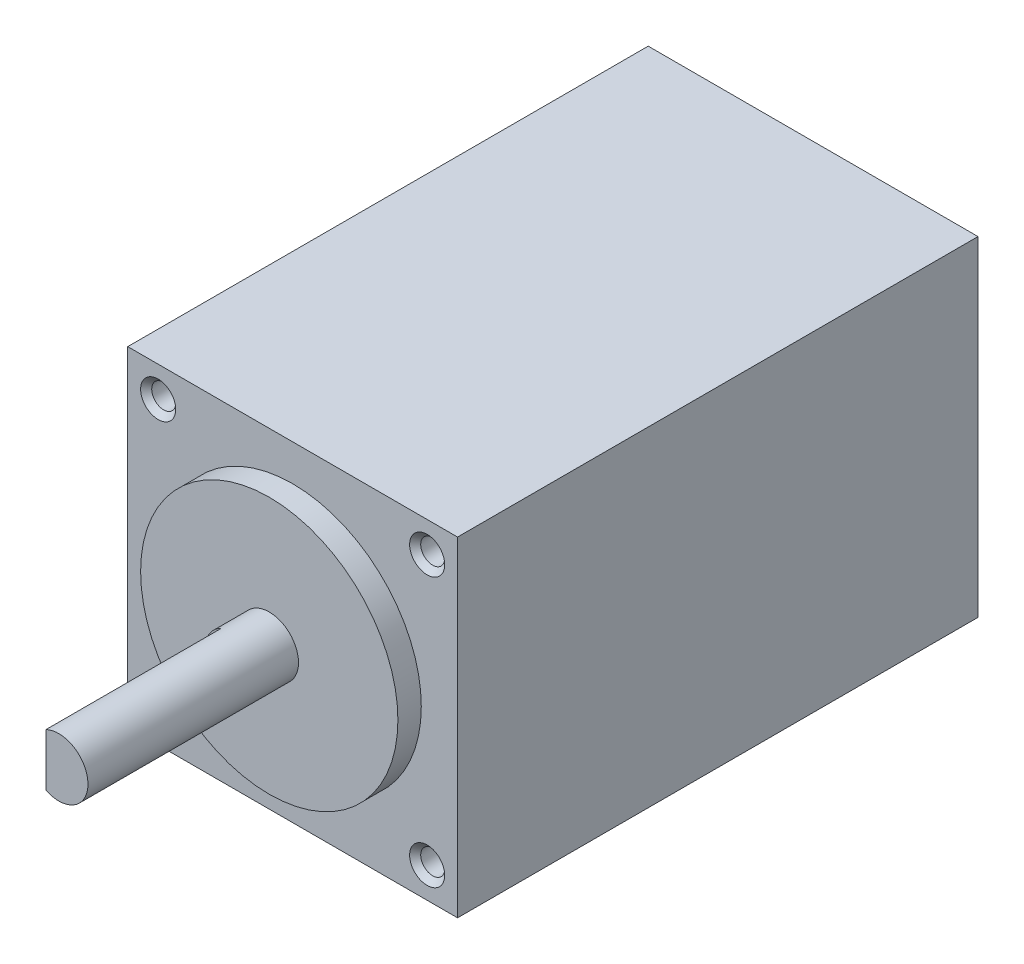
SolidWorks part; units mm, degrees
ref_plane "Front Plane" through (0, 0, 0) normal (0, 0, 1) x (1, 0, 0)
ref_plane "Top Plane" through (0, 0, 0) normal (0, 1, 0) x (1, 0, 0)
ref_plane "Right Plane" through (0, 0, 0) normal (1, 0, 0) x (0, 0, -1)
sketch "Sketch1" plane through (0, 0, 0) normal (0, 0, 1) x (1, 0, 0)
  line L1 (0, 0) -> (28.2, 0)
  line L2 (0, 0) -> (0, 28.2)
  line L3 (0, 28.2) -> (28.2, 28.2)
  line L4 (28.2, 0) -> (28.2, 28.2)
  dimension "D1" = 28.2
  dimension "D2" = 28.2
extrude "Boss-Extrude1" add sketch "Sketch1" along normal blind 44.5
hole_wizard "M2.5x0.45 Tapped Hole1" positions "Sketch2" profile "Sketch4" tap size "M2.5x0.45" standard "ANSI Metric"
sketch "Sketch2" plane through (0, 0, 44.5) normal (0, 0, 1) x (1, 0, 0)
  line L0 (0, 28.2) -> (28.2, 0) construction
  line L3 (2.6, 2.6) -> (25.6, 2.6) construction
  line L4 (2.6, 2.6) -> (2.6, 25.6) construction
  line L5 (2.6, 25.6) -> (25.6, 25.6) construction
  line L6 (25.6, 2.6) -> (25.6, 25.6) construction
  line L7 (2.6, 2.6) -> (25.6, 25.6) construction
  line L8 (2.6, 25.6) -> (25.6, 2.6) construction
  line L9 (0, 28.2) -> (0, 0) construction
  point P8 (25.6, 25.6)
  point P147 (2.6, 2.6)
  point P148 (2.6, 25.6)
  point P149 (25.6, 2.6)
  dimension "D1" = 23
  dimension "D2" = 2.6
sketch "Sketch4" plane through (25.6, 2.6, 44.5) normal (1, 0, 0) x (0, -1, 0)
  line L0 (0, 0) -> (0, 7.0159)
  line L1 (0, 7.0159) -> (1.025, 6.4)
  line L2 (1.025, 6.4) -> (1.025, 0.475)
  line L3 (1.025, 0.475) -> (1.5, 0)
  line L5 (1.5, 0) -> (0, 0)
  line L6 (-1.025, 0.475) -> (-1.5, 0) construction
  line L10 (0, 7.0159) -> (-1.025, 6.4) construction
  line L11 (0, -6.35) -> (0, 107.95) construction
  dimension "Tap Drill Dia." = 2.05
  dimension "Tap Drill Depth" = 6.4
  dimension "Near C'Sink Dia." = 3
  dimension "Near C'Sink Angle" = 90
  dimension "Drill Angle" = 118
cosmetic thread "Hole Thread1" parameters "D1"=5.08, "D2"=2.5
cosmetic thread "Hole Thread2" parameters "D1"=5.08, "D2"=2.5
cosmetic thread "Hole Thread3" parameters "D1"=5.08, "D2"=2.5
cosmetic thread "Hole Thread4" parameters "D1"=5.08, "D2"=2.5
sketch "Sketch15" plane through (0, 0, 44.5) normal (0, 0, 1) x (1, 0, 0)
  line L0 (0, 28.2) -> (28.2, 0) construction
  circle A0 centre (14.1, 14.1) radius 11
  dimension "D1" = 22
extrude "Boss-Extrude2" add sketch "Sketch15" along normal blind 2
sketch "Sketch16" plane through (0, 0, 46.5) normal (0, 0, 1) x (1, 0, 0)
  circle A0 centre (14.1, 14.1) radius 2.5
  dimension "D1" = 5
extrude "Boss-Extrude3" add sketch "Sketch16" along normal blind 18
sketch "Sketch17" plane through (0, 0, 64.5) normal (0, 0, 1) x (1, 0, 0)
  line L0 (13.0103, 16.35) -> (13.0103, 11.85)
  circle A0 centre (14.1, 14.1) radius 2.5 construction
  arc A1 (13.0103, 16.35) -> (13.0103, 11.85) centre (14.1, 14.1) ccw
  dimension "D1" = 4.5
extrude "Cut-Extrude1" cut sketch "Sketch17" against normal blind 15
fillet "Fillet1" [suppressed] radius 1.27
chamfer "Chamfer1" [suppressed] distance 0.254 angle 45
fillet "Fillet2" [suppressed] radius 1.27
